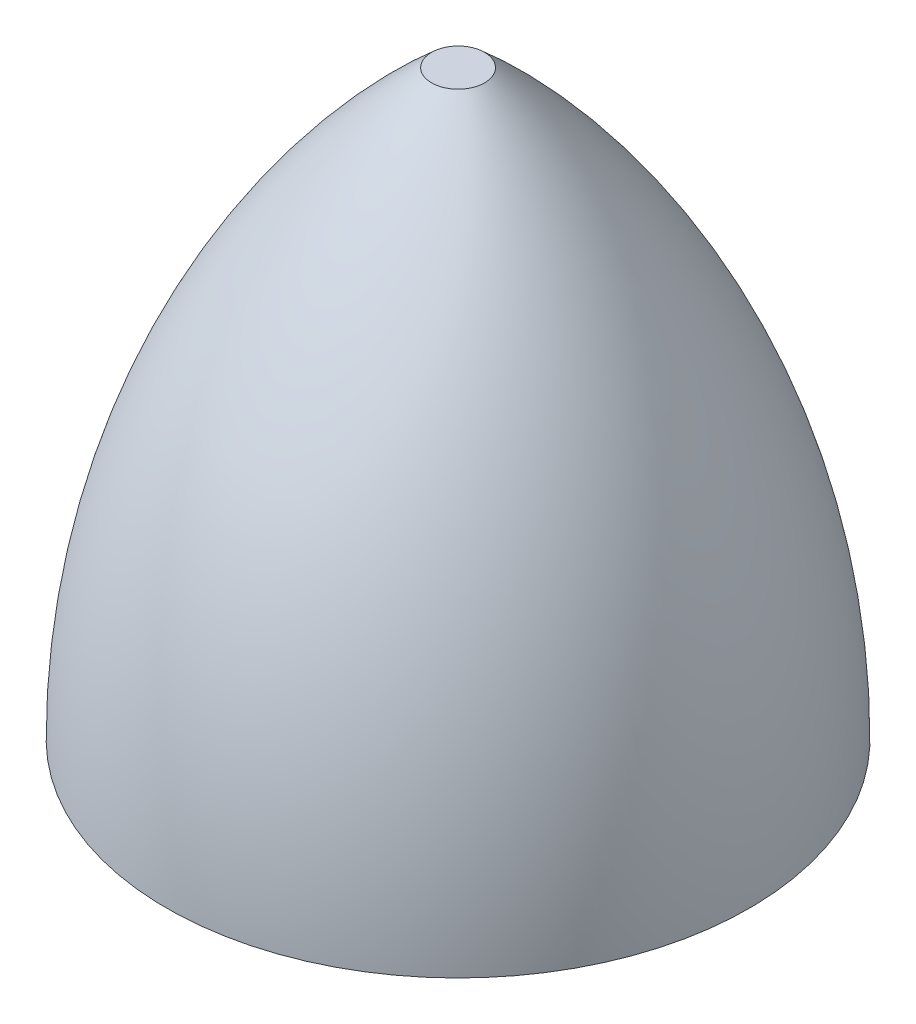
SolidWorks part; units mm, degrees
ref_plane "Plano frontal" through (0, 0, 0) normal (0, 0, 1) x (1, 0, 0)
ref_plane "Plano superior" through (0, 0, 0) normal (0, 1, 0) x (1, 0, 0)
ref_plane "Plano direito" through (0, 0, 0) normal (1, 0, 0) x (0, 0, -1)
sketch "Esboço1" plane through (0, 0, 0) normal (0, 0, 1) x (1, 0, 0)
  line L0 (0, 0) -> (110, 0) construction
  line L1 (0, 0) -> (0, 244.1789) construction
  line L7 (0, 0) -> (110, 0)
  line L9 (10, 220) -> (0, 220)
  line L10 (0, 220) -> (0, 0)
  arc A2 (110, 0) -> (10, 220) centre (-182, 0) ccw
  dimension "D1" = 220
  dimension "D2" = 20
  dimension "D3" = 220
revolve "Revolução2" add sketch "Esboço1" angle 360 about L1
